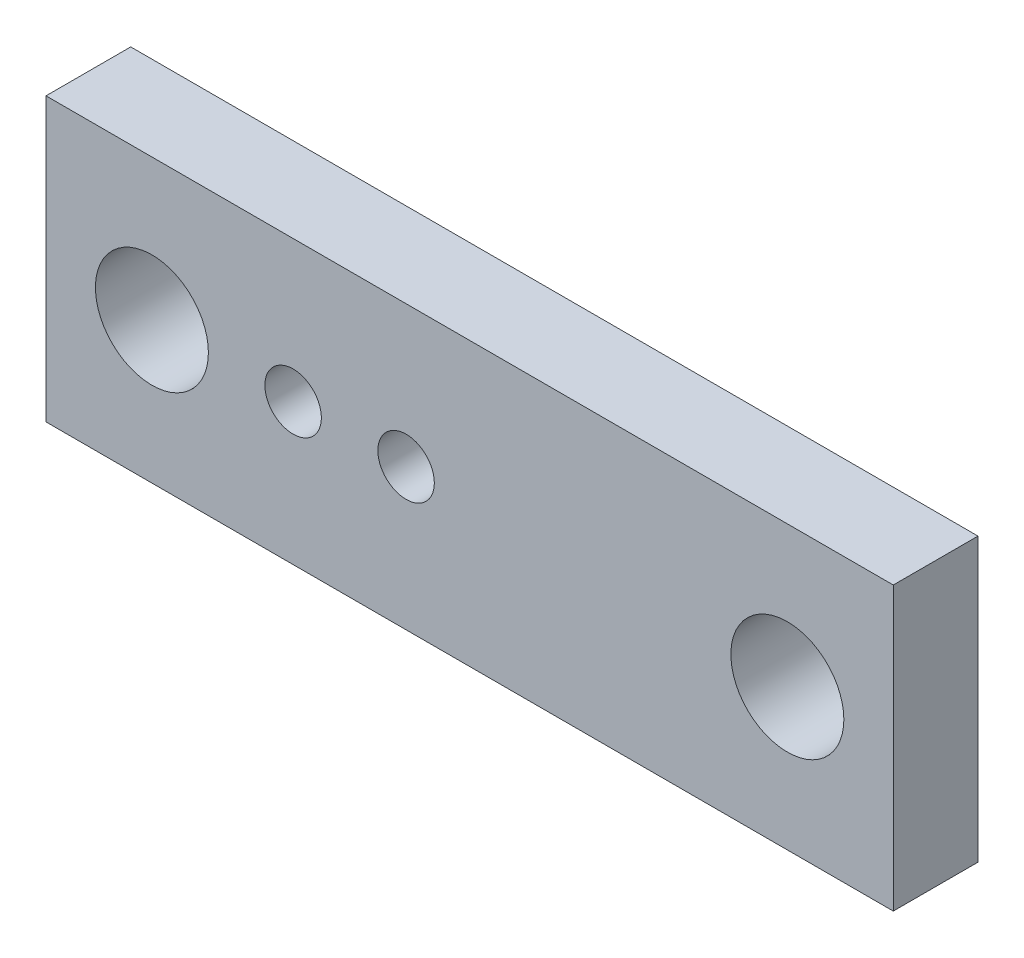
SolidWorks part; units mm, degrees
ref_plane "前基準面" through (0, 0, 0) normal (0, 0, 1) x (1, 0, 0)
ref_plane "上基準面" through (0, 0, 0) normal (0, 1, 0) x (1, 0, 0)
ref_plane "右基準面" through (0, 0, 0) normal (1, 0, 0) x (0, 0, -1)
sketch "草圖1" plane through (0, 0, 0) normal (0, 0, 1) x (1, 0, 0)
  line L0 (0, 10) -> (60, 10) construction
  line L1 (0, 0) -> (60, 0)
  line L2 (0, 0) -> (0, 20)
  line L3 (0, 20) -> (60, 20)
  line L4 (60, 0) -> (60, 20)
  line L5 (30, 20) -> (30, 0) construction
  circle A0 centre (7.5, 10) radius 4
  circle A1 centre (17.5, 10) radius 2
  circle A2 centre (25.5, 10) radius 2
  circle A3 centre (52.5, 10) radius 4
  dimension "D4" = 8
  dimension "D5" = 4
  dimension "D6" = 4
  dimension "D7" = 8
  dimension "D1" = 20
  dimension "D2" = 60
  dimension "D3" = 4.5
  dimension "D8" = 10
  dimension "D9" = 8
  dimension "D10" = 45
extrude "填料-伸長1" add sketch "草圖1" along normal blind 6 contours L0 L2 L1 L4 A3 A2 A1 A0 | L2 L0 A0 A1 A2 A3 L4 L3
sketch "草圖3" plane through (0, 0, 0) normal (0, 0, -1) x (-1, 0, 0)
  line L0 (-25.5, 10) -> (-17.5, 10) construction
  line L1 (-25.5, 12.75) -> (-17.5, 12.75)
  line L2 (-25.5, 7.25) -> (-17.5, 7.25)
  arc A0 (-25.5, 12.75) -> (-25.5, 7.25) centre (-25.5, 10) ccw
  arc A1 (-17.5, 7.25) -> (-17.5, 12.75) centre (-17.5, 10) ccw
  point P4 (-21.5, 10)
  dimension "D1" = 5.5
extrude "除料-伸長1" cut sketch "草圖3" against normal blind 3
